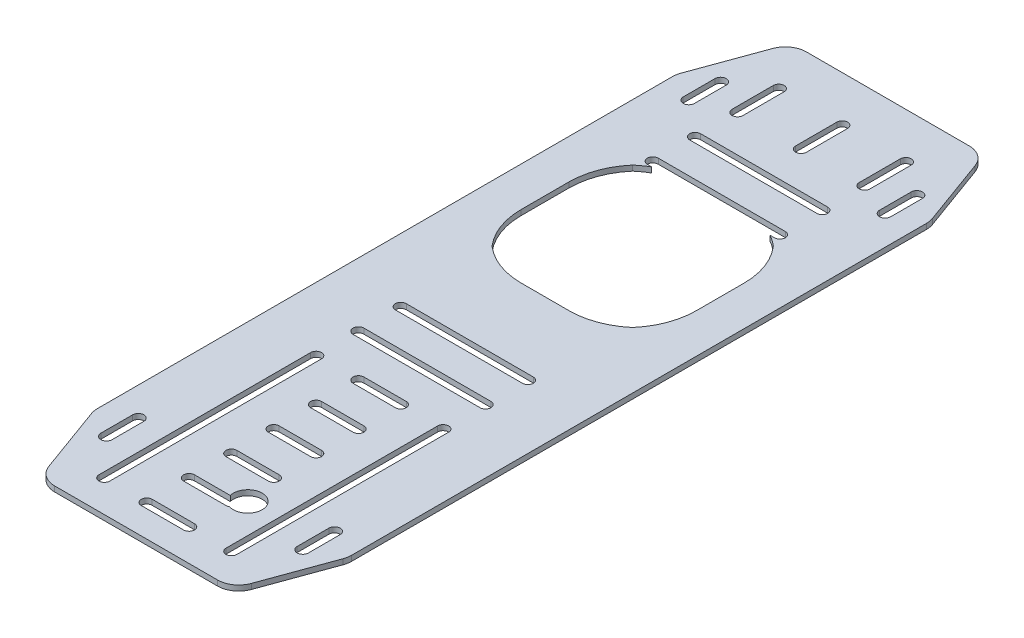
SolidWorks part; units mm, degrees
material "6061-T6 (SS)"
ref_plane "Front Plane" through (0, 0, 0) normal (0, 0, 1) x (1, 0, 0)
ref_plane "Top Plane" through (0, 0, 0) normal (0, 1, 0) x (1, 0, 0)
ref_plane "Right Plane" through (0, 0, 0) normal (1, 0, 0) x (0, 0, -1)
sketch "Sketch1" plane through (0, 0, 0) normal (0, 1, 0) x (1, 0, 0)
  line L0 (0, 495.0997) -> (0, -495.0997) construction
  line L8 (76.2, 330.2) -> (-76.2, 330.2)
  line L9 (76.2, 330.2) -> (76.2, -330.2)
  line L10 (76.2, -330.2) -> (-76.2, -330.2)
  line L11 (-76.2, 330.2) -> (-76.2, -330.2)
  line L12 (76.2, 330.2) -> (-76.2, -330.2) construction
  line L13 (76.2, -330.2) -> (-76.2, 330.2) construction
  point P7 (0, 0)
  dimension "D1" = 660.4
  dimension "D2" = 152.4
extrude "Boss-Extrude1" add sketch "Sketch1" along normal blind 3.18
sketch "Sketch5" plane through (0, 0, 0) normal (0, -1, 0) x (1, 0, 0)
  line L0 (76.2, 279.4) -> (57.7103, 330.2)
  line L1 (76.2, 330.2) -> (76.2, -330.2) construction
  line L2 (-76.2, 330.2) -> (76.2, 330.2) construction
  line L3 (57.7103, 330.2) -> (76.2, 330.2)
  line L4 (76.2, 330.2) -> (76.2, 279.4)
  line L5 (0, -1.749) -> (0, 1.749) construction
  line L6 (-57.7103, 330.2) -> (-76.2, 330.2)
  line L7 (-76.2, 279.4) -> (-57.7103, 330.2)
  line L8 (-76.2, 330.2) -> (-76.2, 279.4)
  line L9 (1.749, 0) -> (-1.749, 0) construction
  line L10 (-76.2, -279.4) -> (-57.7103, -330.2)
  line L11 (-76.2, -330.2) -> (-76.2, -279.4)
  line L12 (-57.7103, -330.2) -> (-76.2, -330.2)
  line L13 (57.7103, -330.2) -> (76.2, -330.2)
  line L14 (76.2, -279.4) -> (57.7103, -330.2)
  line L15 (76.2, -330.2) -> (76.2, -279.4)
  dimension "D1" = 20
  dimension "D2" = 50.8
sketch "Sketch3" plane through (0, 3.18, 0) normal (0, 1, 0) x (1, 0, 0)
  line L0 (-38.1, -101.6) -> (38.1, -101.6) construction
  line L1 (-76.2, -330.2) -> (76.2, -330.2) construction
  line L2 (-38.1, 50.8) -> (38.1, 50.8) construction
  line L5 (-38.1, 54.0639) -> (38.1, 54.0639)
  line L6 (0, -330.2) -> (0, 330.2) construction
  line L7 (-76.2, -330.2) -> (76.2, -330.2) construction
  line L8 (76.2, 330.2) -> (-76.2, 330.2) construction
  line L9 (-38.1, 47.5361) -> (38.1, 47.5361)
  line L12 (-76.2, 0) -> (76.2, 0) construction
  line L13 (-76.2, 330.2) -> (-76.2, -330.2) construction
  line L14 (76.2, -330.2) -> (76.2, 330.2) construction
  line L15 (-38.1, 25.4) -> (-38.1, -101.6) construction
  line L16 (-41.3639, 25.4) -> (-41.3639, -101.6)
  line L17 (-34.8361, 25.4) -> (-34.8361, -101.6)
  line L18 (38.1, 25.4) -> (38.1, -101.6) construction
  line L19 (41.3639, 25.4) -> (41.3639, -101.6)
  line L20 (34.8361, 25.4) -> (34.8361, -101.6)
  line L21 (-76.2, -38.1) -> (76.2, -38.1) construction
  line L22 (-76.2, 330.2) -> (-76.2, -330.2) construction
  line L23 (76.2, -330.2) -> (76.2, 330.2) construction
  line L24 (-38.1, -127) -> (38.1, -127) construction
  line L25 (-38.1, -130.2639) -> (38.1, -130.2639)
  line L26 (-38.1, -123.7361) -> (38.1, -123.7361)
  line L27 (-76.2, -127) -> (76.2, -127) construction
  line L28 (38.1, -279.4) -> (38.1, -152.4) construction
  line L29 (41.3639, -279.4) -> (41.3639, -152.4)
  line L30 (34.8361, -279.4) -> (34.8361, -152.4)
  line L31 (-38.1, -279.4) -> (-38.1, -152.4) construction
  line L32 (-41.3639, -279.4) -> (-41.3639, -152.4)
  line L33 (-34.8361, -279.4) -> (-34.8361, -152.4)
  line L34 (-76.2, -215.9) -> (76.2, -215.9) construction
  line L35 (-38.1, -304.8) -> (38.1, -304.8) construction
  line L36 (-38.1, -301.5361) -> (38.1, -301.5361)
  line L37 (-38.1, -308.0639) -> (38.1, -308.0639)
  line L38 (-12.7, -279.4) -> (12.7, -279.4) construction
  line L39 (-12.7, -276.1361) -> (12.7, -276.1361)
  line L40 (-12.7, -282.6639) -> (12.7, -282.6639)
  line L41 (-12.7, -254) -> (12.7, -254) construction
  line L42 (-12.7, -250.7361) -> (12.7, -250.7361)
  line L43 (-12.7, -257.2639) -> (12.7, -257.2639)
  line L44 (-12.7, -228.6) -> (12.7, -228.6) construction
  line L45 (-12.7, -225.3361) -> (12.7, -225.3361)
  line L46 (-12.7, -231.8639) -> (12.7, -231.8639)
  line L47 (-12.7, -203.2) -> (12.7, -203.2) construction
  line L48 (-12.7, -199.9361) -> (12.7, -199.9361)
  line L49 (-12.7, -206.4639) -> (12.7, -206.4639)
  line L50 (-12.7, -177.8) -> (12.7, -177.8) construction
  line L51 (-12.7, -174.5361) -> (12.7, -174.5361)
  line L52 (-12.7, -181.0639) -> (12.7, -181.0639)
  line L53 (-12.7, -152.4) -> (12.7, -152.4) construction
  line L54 (-12.7, -149.1361) -> (12.7, -149.1361)
  line L55 (-12.7, -155.6639) -> (12.7, -155.6639)
  line L56 (-12.7, 25.4) -> (12.7, 25.4) construction
  line L57 (-12.7, 22.1361) -> (12.7, 22.1361)
  line L58 (-12.7, 28.6639) -> (12.7, 28.6639)
  line L59 (-12.7, 0) -> (12.7, 0) construction
  line L60 (-12.7, -3.2639) -> (12.7, -3.2639)
  line L61 (-12.7, 3.2639) -> (12.7, 3.2639)
  line L62 (-12.7, -25.4) -> (12.7, -25.4) construction
  line L63 (-12.7, -28.6639) -> (12.7, -28.6639)
  line L64 (-12.7, -22.1361) -> (12.7, -22.1361)
  line L65 (-12.7, -50.8) -> (12.7, -50.8) construction
  line L66 (-12.7, -54.0639) -> (12.7, -54.0639)
  line L67 (-12.7, -47.5361) -> (12.7, -47.5361)
  line L68 (-12.7, -76.2) -> (12.7, -76.2) construction
  line L69 (-12.7, -79.4639) -> (12.7, -79.4639)
  line L70 (-12.7, -72.9361) -> (12.7, -72.9361)
  line L71 (-12.7, -101.6) -> (12.7, -101.6) construction
  line L72 (-12.7, -104.8639) -> (12.7, -104.8639)
  line L73 (-12.7, -98.3361) -> (12.7, -98.3361)
  line L74 (-76.2, 63.5) -> (76.2, 63.5) construction
  line L75 (-38.1, 76.2) -> (38.1, 76.2) construction
  line L76 (-38.1, 72.9361) -> (38.1, 72.9361)
  line L77 (-38.1, 79.4639) -> (38.1, 79.4639)
  line L78 (-76.2, 151.7678) -> (76.2, 151.7678) construction
  line L79 (76.2, 330.2) -> (-76.2, 330.2) construction
  line L80 (-38.1, 227.3356) -> (38.1, 227.3356) construction
  line L81 (-38.1, 230.5995) -> (38.1, 230.5995)
  line L82 (-38.1, 224.0717) -> (38.1, 224.0717)
  line L83 (-38.1, 252.7356) -> (38.1, 252.7356) construction
  line L84 (-38.1, 249.4717) -> (38.1, 249.4717)
  line L85 (-38.1, 255.9995) -> (38.1, 255.9995)
  line L86 (-38.1, 302.8393) -> (-38.1, 278.1356) construction
  line L87 (-34.8361, 302.8393) -> (-34.8361, 278.1356)
  line L88 (-41.3639, 302.8393) -> (-41.3639, 278.1356)
  line L89 (0, 302.8393) -> (0, 278.1356) construction
  line L90 (3.2639, 302.8393) -> (3.2639, 278.1356)
  line L91 (-3.2639, 302.8393) -> (-3.2639, 278.1356)
  line L92 (38.1, 302.8393) -> (38.1, 278.1356) construction
  line L93 (41.3639, 302.8393) -> (41.3639, 278.1356)
  line L94 (34.8361, 302.8393) -> (34.8361, 278.1356)
  arc A4 (-41.3639, 25.4) -> (-34.8361, 25.4) centre (-38.1, 25.4) cw
  arc A5 (-34.8361, -101.6) -> (-41.3639, -101.6) centre (-38.1, -101.6) cw
  arc A6 (41.3639, 25.4) -> (34.8361, 25.4) centre (38.1, 25.4) ccw
  arc A7 (34.8361, -101.6) -> (41.3639, -101.6) centre (38.1, -101.6) ccw
  arc A8 (-38.1, 54.0639) -> (-38.1, 47.5361) centre (-38.1, 50.8) ccw
  arc A9 (38.1, 47.5361) -> (38.1, 54.0639) centre (38.1, 50.8) ccw
  arc A10 (-38.1, -130.2639) -> (-38.1, -123.7361) centre (-38.1, -127) cw
  arc A11 (38.1, -123.7361) -> (38.1, -130.2639) centre (38.1, -127) cw
  arc A12 (41.3639, -279.4) -> (34.8361, -279.4) centre (38.1, -279.4) cw
  arc A13 (34.8361, -152.4) -> (41.3639, -152.4) centre (38.1, -152.4) cw
  arc A14 (-41.3639, -279.4) -> (-34.8361, -279.4) centre (-38.1, -279.4) ccw
  arc A15 (-34.8361, -152.4) -> (-41.3639, -152.4) centre (-38.1, -152.4) ccw
  arc A16 (-38.1, -301.5361) -> (-38.1, -308.0639) centre (-38.1, -304.8) ccw
  arc A17 (38.1, -308.0639) -> (38.1, -301.5361) centre (38.1, -304.8) ccw
  arc A18 (-12.7, -276.1361) -> (-12.7, -282.6639) centre (-12.7, -279.4) ccw
  arc A19 (12.7, -282.6639) -> (12.7, -276.1361) centre (12.7, -279.4) ccw
  arc A20 (-12.7, -250.7361) -> (-12.7, -257.2639) centre (-12.7, -254) ccw
  arc A21 (12.7, -257.2639) -> (12.7, -250.7361) centre (12.7, -254) ccw
  arc A22 (-12.7, -225.3361) -> (-12.7, -231.8639) centre (-12.7, -228.6) ccw
  arc A23 (12.7, -231.8639) -> (12.7, -225.3361) centre (12.7, -228.6) ccw
  arc A24 (-12.7, -199.9361) -> (-12.7, -206.4639) centre (-12.7, -203.2) ccw
  arc A25 (12.7, -206.4639) -> (12.7, -199.9361) centre (12.7, -203.2) ccw
  arc A26 (-12.7, -174.5361) -> (-12.7, -181.0639) centre (-12.7, -177.8) ccw
  arc A27 (12.7, -181.0639) -> (12.7, -174.5361) centre (12.7, -177.8) ccw
  arc A28 (-12.7, -149.1361) -> (-12.7, -155.6639) centre (-12.7, -152.4) ccw
  arc A29 (12.7, -155.6639) -> (12.7, -149.1361) centre (12.7, -152.4) ccw
  arc A30 (-12.7, 22.1361) -> (-12.7, 28.6639) centre (-12.7, 25.4) cw
  arc A31 (12.7, 28.6639) -> (12.7, 22.1361) centre (12.7, 25.4) cw
  arc A32 (-12.7, -3.2639) -> (-12.7, 3.2639) centre (-12.7, 0) cw
  arc A33 (12.7, 3.2639) -> (12.7, -3.2639) centre (12.7, 0) cw
  arc A34 (-12.7, -28.6639) -> (-12.7, -22.1361) centre (-12.7, -25.4) cw
  arc A35 (12.7, -22.1361) -> (12.7, -28.6639) centre (12.7, -25.4) cw
  arc A36 (-12.7, -54.0639) -> (-12.7, -47.5361) centre (-12.7, -50.8) cw
  arc A37 (12.7, -47.5361) -> (12.7, -54.0639) centre (12.7, -50.8) cw
  arc A38 (-12.7, -79.4639) -> (-12.7, -72.9361) centre (-12.7, -76.2) cw
  arc A39 (12.7, -72.9361) -> (12.7, -79.4639) centre (12.7, -76.2) cw
  arc A40 (-12.7, -104.8639) -> (-12.7, -98.3361) centre (-12.7, -101.6) cw
  arc A41 (12.7, -98.3361) -> (12.7, -104.8639) centre (12.7, -101.6) cw
  arc A42 (-38.1, 72.9361) -> (-38.1, 79.4639) centre (-38.1, 76.2) cw
  arc A43 (38.1, 79.4639) -> (38.1, 72.9361) centre (38.1, 76.2) cw
  arc A44 (-38.1, 230.5995) -> (-38.1, 224.0717) centre (-38.1, 227.3356) ccw
  arc A45 (38.1, 224.0717) -> (38.1, 230.5995) centre (38.1, 227.3356) ccw
  arc A46 (-38.1, 249.4717) -> (-38.1, 255.9995) centre (-38.1, 252.7356) cw
  arc A47 (38.1, 255.9995) -> (38.1, 249.4717) centre (38.1, 252.7356) cw
  arc A48 (-34.8361, 302.8393) -> (-41.3639, 302.8393) centre (-38.1, 302.8393) ccw
  arc A49 (-41.3639, 278.1356) -> (-34.8361, 278.1356) centre (-38.1, 278.1356) ccw
  arc A50 (3.2639, 302.8393) -> (-3.2639, 302.8393) centre (0, 302.8393) ccw
  arc A51 (-3.2639, 278.1356) -> (3.2639, 278.1356) centre (0, 278.1356) ccw
  arc A52 (41.3639, 302.8393) -> (34.8361, 302.8393) centre (38.1, 302.8393) ccw
  arc A53 (34.8361, 278.1356) -> (41.3639, 278.1356) centre (38.1, 278.1356) ccw
  point P2 (0, 50.8)
  point P4 (0, -101.6)
  point P26 (0, -127)
  point P36 (-38.1, -38.1)
  point P43 (38.1, -38.1)
  point P55 (38.1, -215.9)
  point P62 (-38.1, -215.9)
  point P71 (0, -304.8)
  point P78 (0, -279.4)
  point P87 (0, -254)
  point P94 (0, -228.6)
  point P101 (0, -203.2)
  point P108 (0, -177.8)
  point P115 (0, -152.4)
  point P121 (0, 25.4)
  point P128 (0, 0)
  point P135 (0, -25.4)
  point P142 (0, -50.8)
  point P149 (0, -76.2)
  point P156 (0, -101.6)
  point P165 (0, 76.2)
  point P176 (0, 227.3356)
  point P183 (0, 252.7356)
  point P190 (-38.1, 290.4874)
  point P197 (0, 290.4874)
  point P205 (38.1, 290.4874)
  dimension "D1" = 3.2639
  dimension "D2" = 76.2
  dimension "D5" = 3.2639
  dimension "D7" = 3.2639
  dimension "D14" = 3.2639
  dimension "D3" = 228.6
  dimension "D4" = 127
  dimension "D6" = 25.4
  dimension "D8" = 25.4
  dimension "D9" = 6
  dimension "D10" = 25.4
  dimension "D11" = 12.7
  dimension "D12" = 50.1037
  dimension "7.02489" = 178.4322
  dimension "D13" = 25.4
  dimension "D16" = 38.1
  dimension "D15" = 3
extrude "Cut-Extrude2" cut sketch "Sketch3" against normal through all
sketch "Sketch4" plane through (0, 3.18, 0) normal (0, 1, 0) x (1, 0, 0)
  line L47 (-14.3614, 124.6113) -> (14.3614, 124.6113)
  line L48 (52.54, 162.7899) -> (52.54, 191.5127)
  line L49 (14.3614, 229.6913) -> (-14.3614, 229.6913)
  line L50 (-52.54, 191.5127) -> (-52.54, 162.7899)
  line L51 (-14.3614, 124.6113) -> (14.3614, 124.6113)
  line L52 (52.54, 162.7899) -> (52.54, 191.5127)
  line L53 (14.3614, 229.6913) -> (-14.3614, 229.6913)
  line L54 (-52.54, 191.5127) -> (-52.54, 162.7899)
  arc A93 (-42.1819, 134.9694) -> (-14.3614, 124.6113) centre (-14.3614, 167.1513) ccw
  arc A94 (14.3614, 124.6113) -> (42.1819, 134.9694) centre (14.3614, 167.1513) ccw
  arc A95 (42.1819, 134.9694) -> (52.54, 162.7899) centre (10, 162.7899) ccw
  arc A96 (52.54, 191.5127) -> (42.1819, 219.3332) centre (10, 191.5127) ccw
  arc A97 (42.1819, 219.3332) -> (14.3614, 229.6913) centre (14.3614, 187.1513) ccw
  arc A98 (-14.3614, 229.6913) -> (-42.1819, 219.3332) centre (-14.3614, 187.1513) ccw
  arc A99 (-42.1819, 219.3332) -> (-52.54, 191.5127) centre (-10, 191.5127) ccw
  arc A100 (-52.54, 162.7899) -> (-42.1819, 134.9694) centre (-10, 162.7899) ccw
  arc A101 (-42.1819, 134.9694) -> (-14.3614, 124.6113) centre (-14.3614, 167.1513) ccw
  arc A102 (14.3614, 124.6113) -> (42.1819, 134.9694) centre (14.3614, 167.1513) ccw
  arc A103 (42.1819, 134.9694) -> (52.54, 162.7899) centre (10, 162.7899) ccw
  arc A104 (52.54, 191.5127) -> (42.1819, 219.3332) centre (10, 191.5127) ccw
  arc A105 (42.1819, 219.3332) -> (14.3614, 229.6913) centre (14.3614, 187.1513) ccw
  arc A106 (-14.3614, 229.6913) -> (-42.1819, 219.3332) centre (-14.3614, 187.1513) ccw
  arc A107 (-42.1819, 219.3332) -> (-52.54, 191.5127) centre (-10, 191.5127) ccw
  arc A108 (-52.54, 162.7899) -> (-42.1819, 134.9694) centre (-10, 162.7899) ccw
  dimension "D1" = 2.54
extrude "Cut-Extrude3" cut sketch "Sketch4" against normal through all
extrude "Cut-Extrude4" cut sketch "Sketch5" against normal through all
fillet "Fillet1" radius 12.7 8 edges at (-76.2, 1.59, -279.4) (-57.7103, 1.59, -330.2) (57.7103, 1.59, -330.2) (76.2, 1.59, -279.4) (76.2, 1.59, 279.4) (57.7103, 1.59, 330.2) (-57.7103, 1.59, 330.2) (-76.2, 1.59, 279.4)
sketch "Sketch6" plane through (0, 3.18, 0) normal (0, 1, 0) x (1, 0, 0)
  circle A1 centre (17.106, -70.8034) radius 8.636 construction
  circle A2 centre (17.106, -70.8034) radius 8.636
extrude "Cut-Extrude5" cut sketch "Sketch6" along normal through all and the other way through all
sketch "Sketch7" plane through (0, 0, 0) normal (0, -1, 0) x (1, 0, 0)
  line L0 (76.2, 330.2) -> (76.2, 120.65)
  line L1 (76.2, 277.1606) -> (76.2, -277.1606) construction
  line L2 (76.2, 120.65) -> (-76.2, 120.65)
  line L3 (-76.2, 120.65) -> (-76.2, 330.2)
  line L4 (-76.2, -277.1606) -> (-76.2, 277.1606) construction
  line L5 (-76.2, 330.2) -> (76.2, 330.2)
  line L6 (-48.8177, 330.2) -> (48.8177, 330.2) construction
  dimension "D1" = 209.55
extrude "Cut-Extrude6" cut sketch "Sketch7" against normal up to next
sketch "Sketch8" plane through (0, 0, 0) normal (0, -1, 0) x (1, 0, 0)
  line L0 (76.2, 69.85) -> (76.2, 120.65)
  line L1 (76.2, 120.65) -> (76.2, -277.1606) construction
  line L2 (76.2, 120.65) -> (57.7103, 120.65)
  line L3 (-76.2, 120.65) -> (76.2, 120.65) construction
  line L4 (57.7103, 120.65) -> (76.2, 69.85)
  line L5 (0, -330.2) -> (0, 120.65) construction
  line L6 (48.8177, -330.2) -> (-48.8177, -330.2) construction
  line L7 (-76.2, 120.65) -> (-57.7103, 120.65)
  line L8 (-76.2, 69.85) -> (-76.2, 120.65)
  line L9 (-57.7103, 120.65) -> (-76.2, 69.85)
  dimension "D1" = 50.8
  dimension "D2" = 20
extrude "Cut-Extrude7" cut sketch "Sketch8" against normal up to next
fillet "Fillet2" radius 12.7 4 edges at (57.7103, 1.59, 120.65) (76.2, 1.59, 69.85) (-57.7103, 1.59, 120.65) (-76.2, 1.59, 69.85)
sketch "Sketch9" plane through (0, 0, 0) normal (0, -1, 0) x (1, 0, 0)
  line L0 (58.674, -269.875) -> (58.674, -288.925) construction
  line L1 (62.0522, -269.875) -> (62.0522, -288.925)
  line L2 (55.2958, -269.875) -> (55.2958, -288.925)
  line L3 (-59.0358, -269.875) -> (-59.0358, -288.925) construction
  line L4 (-55.6576, -269.875) -> (-55.6576, -288.925)
  line L5 (-62.414, -269.875) -> (-62.414, -288.925)
  line L6 (76.2, -104.775) -> (-76.2, -104.775) construction
  line L7 (76.2, 67.6106) -> (76.2, -277.1606) construction
  line L8 (-76.2, -277.1606) -> (-76.2, 67.6106) construction
  line L9 (-59.0358, 60.325) -> (-59.0358, 79.375) construction
  line L12 (-55.6576, 60.325) -> (-55.6576, 79.375)
  line L15 (58.674, -279.4) -> (-59.0358, -279.4) construction
  line L16 (48.8177, -330.2) -> (-48.8177, -330.2) construction
  line L17 (-62.414, 60.325) -> (-62.414, 79.375)
  line L18 (58.674, 60.325) -> (58.674, 79.375) construction
  line L19 (62.0522, 60.325) -> (62.0522, 79.375)
  line L20 (55.2958, 60.325) -> (55.2958, 79.375)
  arc A0 (62.0522, -269.875) -> (55.2958, -269.875) centre (58.674, -269.875) ccw
  arc A1 (55.2958, -288.925) -> (62.0522, -288.925) centre (58.674, -288.925) ccw
  arc A2 (-55.6576, 60.325) -> (-62.414, 60.325) centre (-59.0358, 60.325) cw
  arc A3 (-55.6576, -269.875) -> (-62.414, -269.875) centre (-59.0358, -269.875) ccw
  arc A4 (-62.414, -288.925) -> (-55.6576, -288.925) centre (-59.0358, -288.925) ccw
  arc A5 (-62.414, 79.375) -> (-55.6576, 79.375) centre (-59.0358, 79.375) cw
  arc A10 (62.0522, 60.325) -> (55.2958, 60.325) centre (58.674, 60.325) cw
  arc A11 (55.2958, 79.375) -> (62.0522, 79.375) centre (58.674, 79.375) cw
  point P3 (58.674, -279.4)
  point P13 (-59.0358, -279.4)
  point P27 (-59.0358, 69.85)
  point P34 (58.674, 69.85)
  dimension "D2" = 3.3782
  dimension "D1" = 19.05
  dimension "D3" = 50.8
  dimension "D4" = 17.1642
  dimension "D5" = 17.526
extrude "Cut-Extrude8" cut sketch "Sketch9" against normal up to next
scale "Scale1" scale about centroid uniform scaling yes scale factor 0.35
